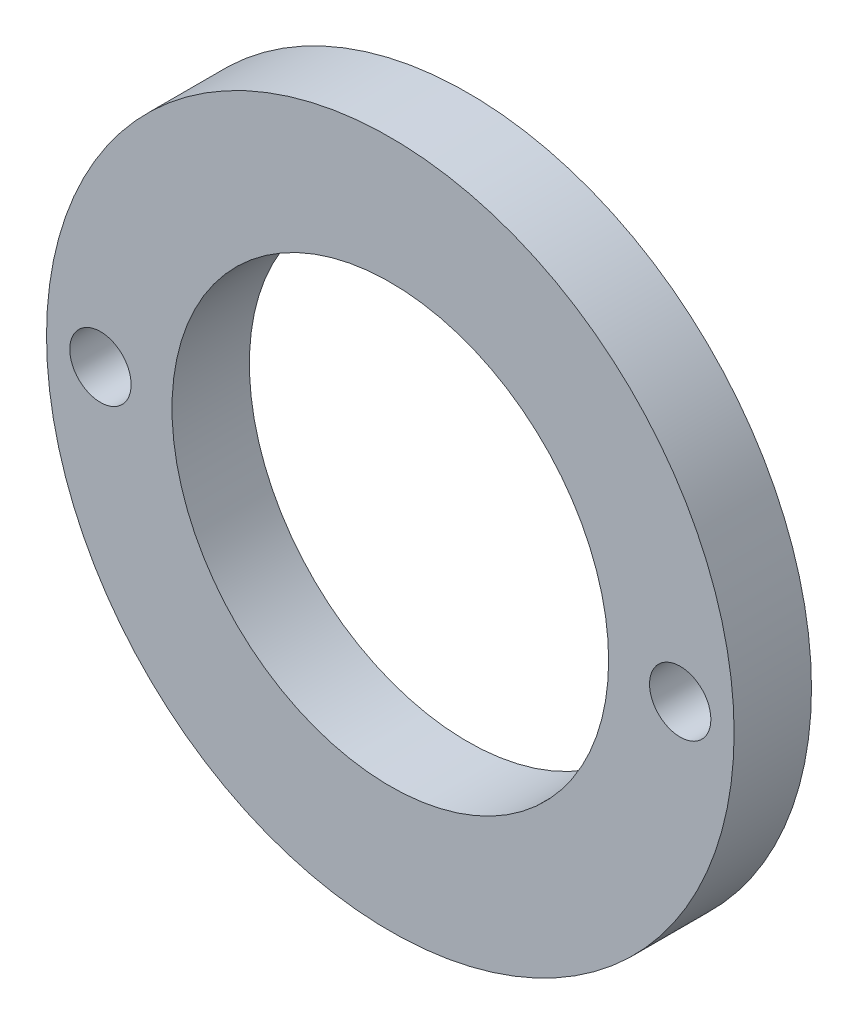
SolidWorks part; units mm, degrees
ref_plane "Front Plane" through (0, 0, 0) normal (0, 0, 1) x (1, 0, 0)
ref_plane "Top Plane" through (0, 0, 0) normal (0, 1, 0) x (1, 0, 0)
ref_plane "Right Plane" through (0, 0, 0) normal (1, 0, 0) x (0, 0, -1)
sketch "Sketch1" plane through (0, 0, 0) normal (0, 0, 1) x (1, 0, 0)
  circle A0 centre (0, 0) radius 20
  circle A1 centre (0, 0) radius 12.7
  dimension "D1" = 25.4
  dimension "D2" = 40
extrude "Boss-Extrude1" add sketch "Sketch1" along normal blind 4.5 contours A0 | A1
hole_wizard "#28 (0.1405) Diameter Hole1" positions "Sketch5" profile "Sketch4" hole size "#28" standard "ANSI Inch" end condition through all
sketch "Sketch5" plane through (0, 0, 4.5) normal (0, 0, 1) x (1, 0, 0)
  point P0 (-16.8627, 0)
  point P3 (16.8627, 0)
  point P6 (16.8627, 0)
sketch "Sketch4" plane through (-16.8627, 0, 4.5) normal (1, 0, 0) x (0, -1, 0)
  line L0 (0, 0) -> (0, 4.5)
  line L1 (0, 4.5) -> (1.7843, 4.5)
  line L2 (1.7843, 4.5) -> (1.7843, 0)
  line L5 (1.7843, 0) -> (0, 0)
  line L11 (0, -6.35) -> (0, 107.95) construction
  dimension "Thru Hole Dia." = 3.5687
  dimension "Thru Hole Depth" = 4.5
